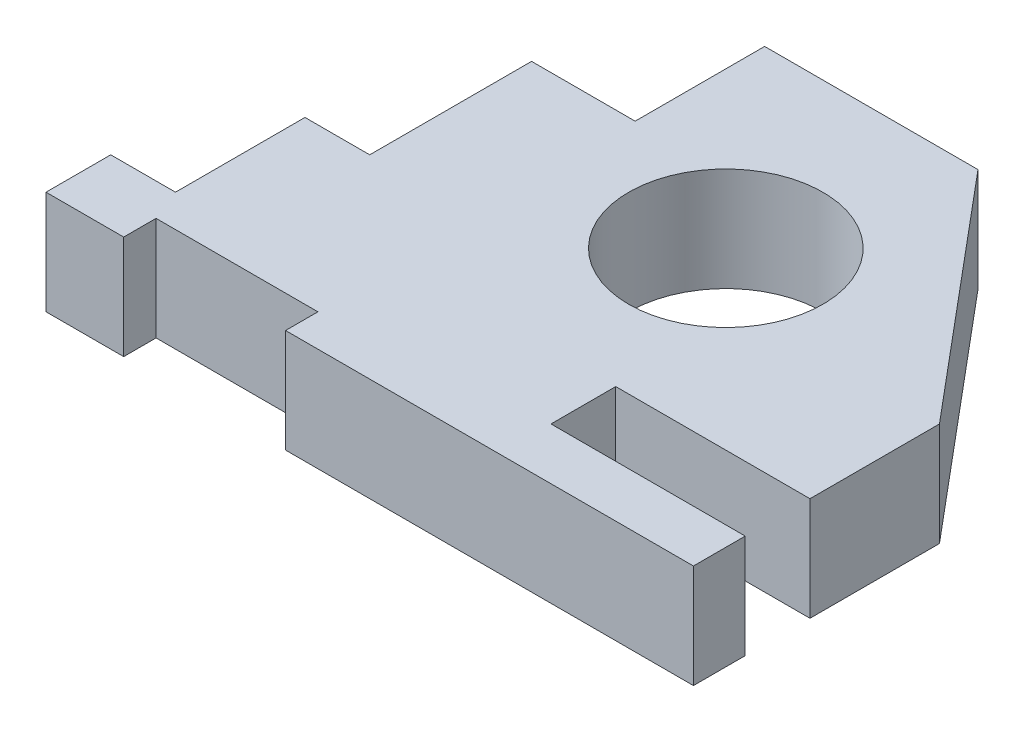
SolidWorks part; units mm, degrees
ref_plane "Front Plane" through (0, 0, 0) normal (0, 0, 1) x (1, 0, 0)
ref_plane "Top Plane" through (0, 0, 0) normal (0, 1, 0) x (1, 0, 0)
ref_plane "Right Plane" through (0, 0, 0) normal (1, 0, 0) x (0, 0, -1)
sketch "Sketch1" plane through (0, 0, 0) normal (0, 1, 0) x (1, 0, 0)
  line L0 (0, 0) -> (12, 0)
  line L1 (12, 0) -> (12, 5)
  line L2 (12, 5) -> (37, 5)
  line L3 (37, 5) -> (37, 0)
  line L4 (37, 0) -> (100, 0)
  line L5 (100, 0) -> (100, 8)
  line L6 (100, 8) -> (70, 8)
  line L7 (70, 8) -> (70, 18)
  line L8 (70, 18) -> (100, 18)
  line L9 (100, 18) -> (100, 38)
  line L10 (0, 0) -> (0, 10)
  line L11 (0, 10) -> (10, 10)
  line L12 (10, 10) -> (10, 30)
  line L13 (10, 30) -> (20, 30)
  line L14 (20, 30) -> (20, 55)
  line L15 (20, 55) -> (36, 55)
  line L16 (36, 55) -> (36, 75)
  line L17 (36, 75) -> (68.9533, 75)
  line L18 (68.9533, 75) -> (100, 38)
  circle A0 centre (60, 45) radius 15
  point P22 (58.045, 75)
  point P23 (105.8143, 33.6525)
  dimension "D17" = 45
  dimension "D20" = 30
  dimension "D1" = 12
  dimension "D2" = 25
  dimension "D3" = 5
  dimension "D4" = 30
  dimension "D5" = 10
  dimension "D6" = 10
  dimension "D7" = 30
  dimension "D8" = 100
  dimension "D9" = 10
  dimension "D10" = 8
  dimension "D11" = 38
  dimension "D12" = 20
  dimension "D13" = 75
  dimension "D14" = 36
  dimension "D15" = 55
  dimension "D16" = 40
  dimension "D18" = 40
  dimension "D19" = 100
extrude "Boss-Extrude1" add sketch "Sketch1" along normal blind 16
